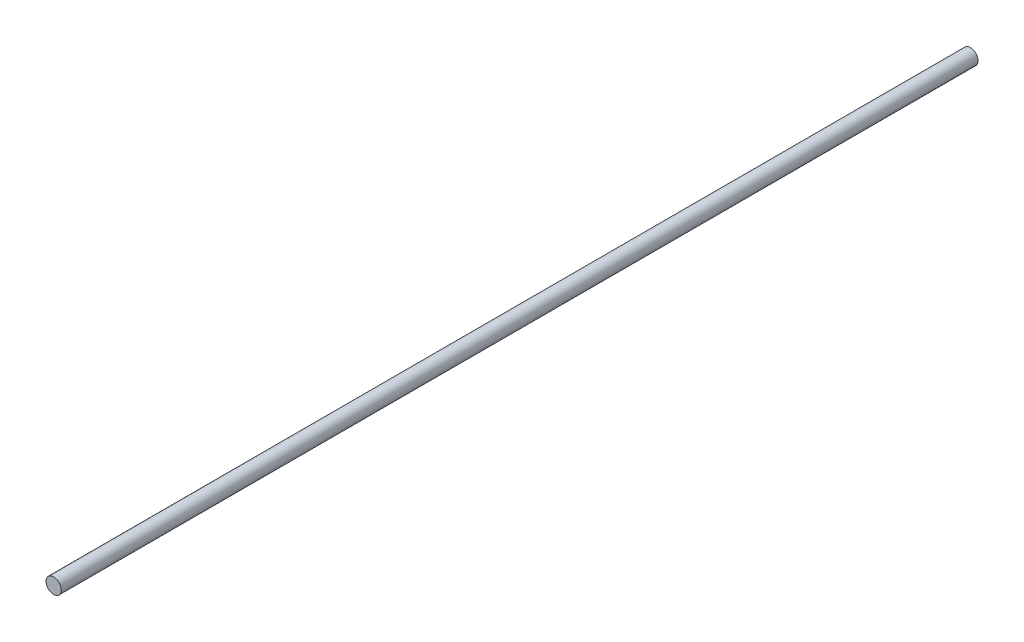
SolidWorks part; units mm, degrees
ref_plane "Alzado" through (0, 0, 0) normal (0, 0, 1) x (1, 0, 0)
ref_plane "Planta" through (0, 0, 0) normal (0, 1, 0) x (1, 0, 0)
ref_plane "Vista lateral" through (0, 0, 0) normal (1, 0, 0) x (0, 0, -1)
sketch "Croquis1" plane through (0, 0, 0) normal (0, 0, 1) x (1, 0, 0)
  circle A0 centre (0, 0) radius 1.5
  dimension "D1" = 3
extrude "Saliente-Extruir1" add sketch "Croquis1" along normal blind 180
